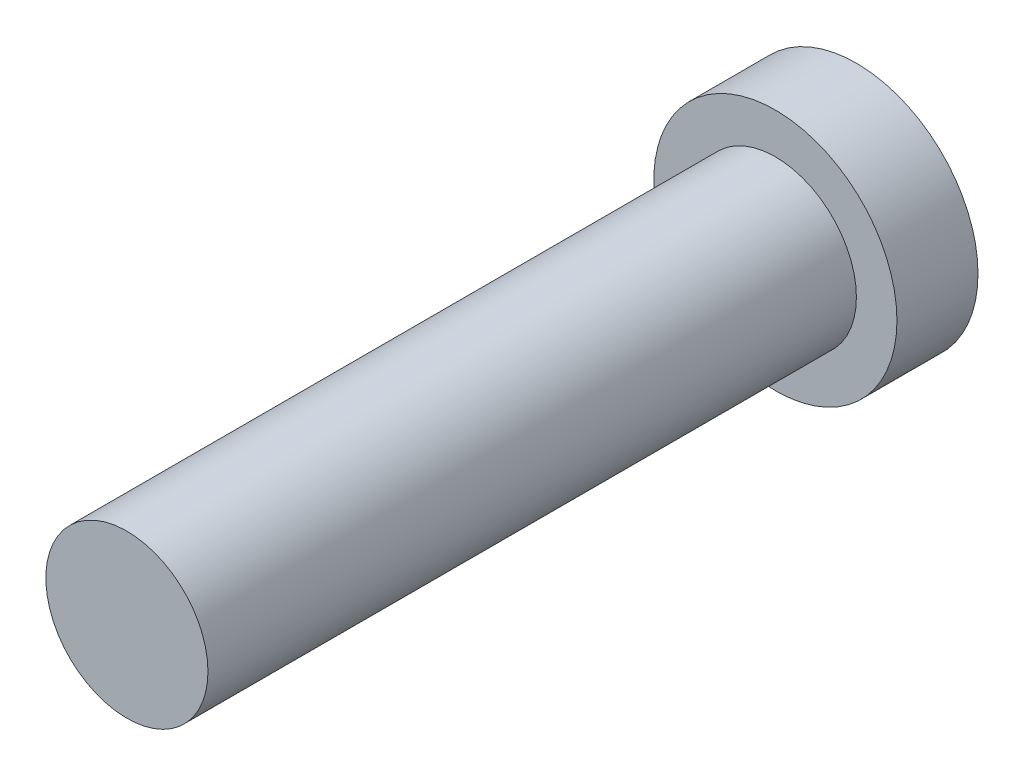
SolidWorks part; units mm, degrees
ref_plane "Front Plane" through (0, 0, 0) normal (0, 0, 1) x (1, 0, 0)
ref_plane "Top Plane" through (0, 0, 0) normal (0, 1, 0) x (1, 0, 0)
ref_plane "Right Plane" through (0, 0, 0) normal (1, 0, 0) x (0, 0, -1)
sketch "Sketch2" plane through (0, 0, 0) normal (0, 0, 1) x (1, 0, 0)
  circle A0 centre (0, 0) radius 19.05
  dimension "D1" = 38.1
extrude "Boss-Extrude1" add sketch "Sketch2" along normal mid plane 12.7
sketch "Sketch3" plane through (0, 0, 6.35) normal (0, 0, 1) x (1, 0, 0)
  circle A0 centre (0, 0) radius 12.7
  dimension "D1" = 25.4
extrude "Boss-Extrude2" add sketch "Sketch3" along normal blind 101.6
